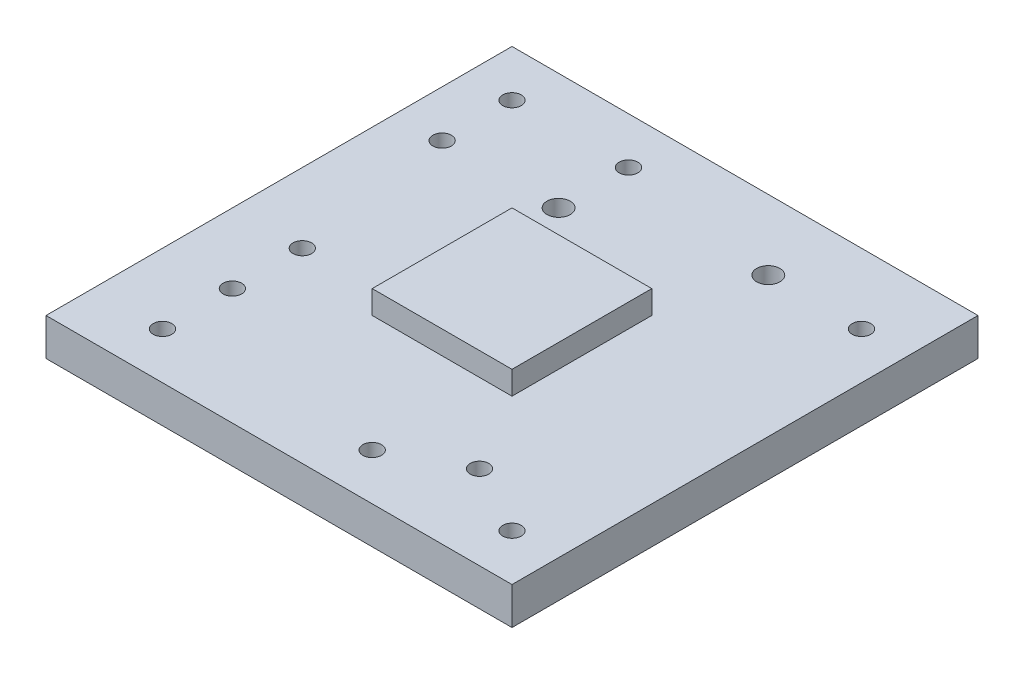
SolidWorks part; units mm, degrees
ref_plane "Front Plane" through (0, 0, 0) normal (0, 0, 1) x (1, 0, 0)
ref_plane "Top Plane" through (0, 0, 0) normal (0, 1, 0) x (1, 0, 0)
ref_plane "Right Plane" through (0, 0, 0) normal (1, 0, 0) x (0, 0, -1)
sketch "Sketch1" plane through (0, 0, 0) normal (0, 1, 0) x (1, 0, 0)
  line L1 (0, 0) -> (100, 0)
  line L2 (0, 0) -> (0, 100)
  line L3 (0, 100) -> (100, 100)
  line L4 (100, 0) -> (100, 100)
  dimension "D1" = 100
  dimension "D2" = 100
extrude "Boss-Extrude1" add sketch "Sketch1" along normal blind 8
sketch "Sketch2" plane through (0, 8, 0) normal (0, 1, 0) x (1, 0, 0)
  line L0 (100, 100) -> (0, 100) construction
  line L1 (35, 35) -> (65, 35)
  line L2 (35, 35) -> (35, 65)
  line L3 (35, 65) -> (65, 65)
  line L4 (65, 35) -> (65, 65)
  line L5 (0, 100) -> (0, 0) construction
  point P4 (50, 65)
  point P7 (50, 100)
  point P8 (35, 50)
  point P11 (0, 50)
  dimension "D1" = 30
  dimension "D2" = 30
  dimension "D3" = 0
  dimension "D4" = 0
extrude "Boss-Extrude2" add sketch "Sketch2" along normal blind 5
sketch "Sketch3" plane through (0, 8, 0) normal (0, 1, 0) x (1, 0, 0)
  line L0 (100, 100) -> (0, 100) construction
  line L1 (0, 100) -> (0, 0) construction
  circle A0 centre (10, 90) radius 2
  circle A1 centre (35, 90) radius 2
  circle A2 centre (10, 75) radius 2
  circle A3 centre (35, 75) radius 2.5
  dimension "D4" = 4
  dimension "D6" = 4
  dimension "D8" = 4
  dimension "D9" = 5
  dimension "D1" = 10
  dimension "D2" = 10
  dimension "D3" = 10
  dimension "D5" = 25
  dimension "D7" = 15
extrude "Cut-Extrude1" cut sketch "Sketch3" against normal blind 19
sketch "Sketch4" plane through (0, 8, 0) normal (0, 1, 0) x (1, 0, 0)
  line L0 (100, 0) -> (100, 100) construction
  line L1 (100, 100) -> (0, 100) construction
  circle A0 centre (90, 85) radius 2
  circle A1 centre (70, 85) radius 2.5
  dimension "D3" = 4
  dimension "D5" = 5
  dimension "D1" = 10
  dimension "D2" = 15
  dimension "D4" = 20
extrude "Cut-Extrude2" cut sketch "Sketch4" against normal blind 19
sketch "Sketch5" plane through (0, 8, 0) normal (0, 1, 0) x (1, 0, 0)
  line L0 (0, 100) -> (0, 0) construction
  line L1 (0, 0) -> (100, 0) construction
  circle A0 centre (15, 10) radius 2
  circle A1 centre (15, 25) radius 2
  circle A2 centre (15, 40) radius 2
  dimension "D3" = 4
  dimension "D6" = 4
  dimension "D7" = 4
  dimension "D1" = 15
  dimension "D2" = 10
  dimension "D4" = 15
  dimension "D5" = 15
extrude "Cut-Extrude3" cut sketch "Sketch5" against normal blind 19
sketch "Sketch6" plane through (0, 8, 0) normal (0, 1, 0) x (1, 0, 0)
  line L0 (0, 0) -> (100, 0) construction
  line L1 (100, 0) -> (100, 100) construction
  circle A0 centre (90, 10) radius 2
  circle A1 centre (60, 10) radius 2
  circle A2 centre (75, 18.0259) radius 2
  point P10 (0, 0)
  point P11 (0, 0)
  dimension "D3" = 4
  dimension "D4" = 4
  dimension "D6" = 4
  dimension "D1" = 10
  dimension "D2" = 10
  dimension "D5" = 30
  dimension "D7" = 15
extrude "Cut-Extrude4" cut sketch "Sketch6" against normal blind 19
